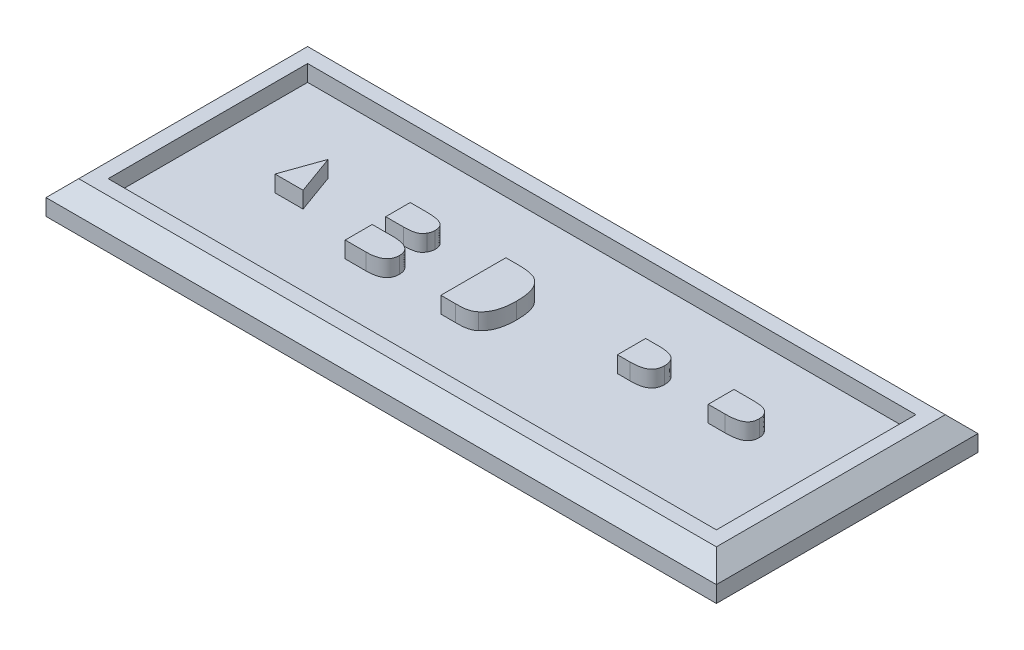
SolidWorks part; units mm, degrees
material "BUTYL"
ref_plane "Front Plane" through (0, 0, 0) normal (0, 0, 1) x (1, 0, 0)
ref_plane "Top Plane" through (0, 0, 0) normal (0, 1, 0) x (1, 0, 0)
ref_plane "Right Plane" through (0, 0, 0) normal (1, 0, 0) x (0, 0, -1)
sketch "Sketch1" plane through (0, 0, 0) normal (0, 1, 0) x (1, 0, 0)
  line L1 (20.5, -8) -> (-20.5, -8)
  line L2 (20.5, -8) -> (20.5, 8)
  line L3 (20.5, 8) -> (-20.5, 8)
  line L4 (-20.5, -8) -> (-20.5, 8)
  line L5 (20.5, -8) -> (-20.5, 8) construction
  line L6 (20.5, 8) -> (-20.5, -8) construction
  point P0 (0, 0)
  dimension "D1" = 41
  dimension "D2" = 16
extrude "Boss-Extrude1" add sketch "Sketch1" along normal blind 2
chamfer "Chamfer1" distance 1 angle 45 4 edges at (0, 2, -8) (20.5, 2, 0) (0, 2, 8) (-20.5, 2, 0)
sketch "Sketch2" plane through (0, 2, 0) normal (0, 1, 0) x (1, 0, 0)
  line L0 (-20.5, 8) -> (20.5, 8) construction
  line L1 (18.6, -6.1) -> (-18.6, -6.1)
  line L2 (18.6, -6.1) -> (18.6, 6.1)
  line L3 (18.6, 6.1) -> (-18.6, 6.1)
  line L4 (-18.6, -6.1) -> (-18.6, 6.1)
  line L5 (18.6, -6.1) -> (-18.6, 6.1) construction
  line L6 (18.6, 6.1) -> (-18.6, -6.1) construction
  line L7 (-20.5, -8) -> (-20.5, 8) construction
  point P0 (0, 0)
  dimension "D1" = 1.9
  dimension "D2" = 1.9
extrude "Cut-Extrude1" cut sketch "Sketch2" against normal blind 1
sketch "Sketch3" plane through (0, 1, 0) normal (0, 1, 0) x (1, 0, 0)
  line L0 (-17.5, -3) -> (17.5, -3) construction
  text T0 "ABDIPR" font "Arial Rounded MT Bold" height 6
  point P3 (0, -3)
  dimension "D1" = 35
  dimension "D2" = 3
extrude "Boss-Extrude2" add sketch "Sketch3" along normal blind 0.1
sketch "Sketch5" plane through (0, 1, 0) normal (0, 1, 0) x (1, 0, 0)
  line L0 (12.7688, 1.875) -> (11.7, 1.875) construction
  line L1 (11.7, 1.875) -> (11.7, 0.3) construction
  line L2 (11.7, 0.3) -> (12.7371, 0.3) construction
  line L3 (-12.8941, 1.65) -> (-13.7437, -0.75)
  line L4 (-13.7437, -0.75) -> (-12.0281, -0.75)
  line L5 (-12.0281, -0.75) -> (-12.8941, 1.65)
  line L6 (-12.8941, 1.65) -> (-13.7437, -0.75)
  line L7 (-13.7437, -0.75) -> (-12.0281, -0.75)
  line L8 (-12.0281, -0.75) -> (-12.8941, 1.65)
  line L9 (7.0793, 1.875) -> (6.3, 1.875) construction
  line L10 (6.3, 1.875) -> (6.3, 0.15) construction
  line L11 (6.3, 0.15) -> (7.0793, 0.15) construction
  line L12 (-1.4648, 1.875) -> (-2.25, 1.875) construction
  line L13 (-2.25, 1.875) -> (-2.25, -2.1) construction
  line L14 (-2.25, -2.1) -> (-1.3488, -2.1) construction
  line L15 (-6.866, -0.45) -> (-8.1, -0.45) construction
  line L16 (-8.1, -0.45) -> (-8.1, -2.1) construction
  line L17 (-8.1, -2.1) -> (-6.8262, -2.1) construction
  line L18 (-7.1367, 1.875) -> (-8.1, 1.875) construction
  line L19 (-8.1, 1.875) -> (-8.1, 0.375) construction
  line L20 (-8.1, 0.375) -> (-7.0137, 0.375) construction
  line L21 (12.7688, 1.875) -> (11.7, 1.875)
  line L22 (11.7, 1.875) -> (11.7, 0.3)
  line L23 (11.7, 0.3) -> (12.7371, 0.3)
  line L24 (7.0793, 1.875) -> (6.3, 1.875)
  line L25 (6.3, 1.875) -> (6.3, 0.15)
  line L26 (6.3, 0.15) -> (7.0793, 0.15)
  line L27 (-1.4648, 1.875) -> (-2.25, 1.875)
  line L28 (-2.25, 1.875) -> (-2.25, -2.1)
  line L29 (-2.25, -2.1) -> (-1.3488, -2.1)
  line L30 (-6.866, -0.45) -> (-8.1, -0.45)
  line L31 (-8.1, -0.45) -> (-8.1, -2.1)
  line L32 (-8.1, -2.1) -> (-6.8262, -2.1)
  line L33 (-7.1367, 1.875) -> (-8.1, 1.875)
  line L34 (-8.1, 1.875) -> (-8.1, 0.375)
  line L35 (-8.1, 0.375) -> (-7.0137, 0.375)
  spline S0 degree 3 poles (636.1641, 1902.3115) (13.4565, -15.0711) (15.9902, 1.1964) (13.4389, 1.8288) (13.3568, 1.8418) (13.2632, 1.8553) (13.1572, 1.8644) (13.0387, 1.8693) (6.9662, 2.1272) (0.5827, -14.141) (37.3484, 2001.6396) knots -9.463288 -9.463288 -9.463288 -9.463288 0.075159 0.163378 0.266297 0.383318 0.514253 0.660795 0.8232 23.058791 23.058791 23.058791 23.058791 only from (13.5691, 1.7895) to (12.7688, 1.875) construction
  spline S1 degree 3 poles (53.3008, -1999.2151) (-1.5912, 19.4596) (6.0427, -0.1571) (13.117, 0.3151) (13.285, 0.3372) (13.4361, 0.3681) (13.572, 0.4091) (13.6895, 0.4663) (13.793, 0.5325) (13.8776, 0.6151) (13.9457, 0.7122) (13.9917, 0.8268) (14.8069, 4.518) (-12.1459, 11.1207) (2003.8058, -199.5267) knots -11.98143 -11.98143 -11.98143 -11.98143 0.116004 0.22342 0.320583 0.409966 0.491045 0.566273 0.636247 0.703392 0.770177 0.84071 0.916405 7.297933 7.297933 7.297933 7.297933 only from (12.7371, 0.3) to (14.025, 1.0969) construction
  spline S2 degree 3 poles (2003.3668, 206.5207) (-10.522, -7.7795) (14.7098, -1.8463) (13.9972, 1.3213) (13.9595, 1.4242) (13.9065, 1.5187) (13.841, 1.6053) (13.7614, 1.6789) (11.1525, 3.5367) (-3.988, -17.2235) (977.1885, 1754.2872) knots -10.607515 -10.607515 -10.607515 -10.607515 0.13182 0.25825 0.380206 0.503359 0.625641 0.747872 0.871018 11.467851 11.467851 11.467851 11.467851 only from (14.025, 1.0969) to (13.5691, 1.7895) construction
  spline S3 degree 3 poles (1232.4253, 1582.9606) (-1.6719, -19.9023) (10.3794, 0.3213) (7.9441, 1.7387) (7.8387, 1.7791) (7.7189, 1.8166) (7.5819, 1.8419) (7.429, 1.862) (0.9477, 2.296) (-5.9865, -17.5415) (37.829, 2001.6036) knots -7.503764 -7.503764 -7.503764 -7.503764 0.084936 0.178562 0.282967 0.398901 0.527506 0.670084 0.828145 18.59632 18.59632 18.59632 18.59632 only from (8.1035, 1.6242) to (7.0793, 1.875) construction
  spline S4 degree 3 poles (51.2137, -1999.2957) (-6.4783, 19.9924) (0.7904, -0.3609) (7.4497, 0.168) (7.6125, 0.1953) (7.7595, 0.2304) (7.8902, 0.2792) (8.004, 0.3433) (8.1028, 0.4193) (8.1839, 0.5104) (8.2491, 0.6153) (8.2923, 0.7364) (9.0939, 4.6114) (-17.4307, 11.3013) (1998.5684, -195.6446) knots -11.235596 -11.235596 -11.235596 -11.235596 0.112942 0.216743 0.311985 0.398388 0.477984 0.552443 0.623708 0.692647 0.762442 0.836024 0.913978 7.58211 7.58211 7.58211 7.58211 only from (7.0793, 0.15) to (8.325, 1.016) construction
  spline S5 degree 3 poles (1992.4694, 252.0641) (-20.7902, -10.8673) (9.3304, -2.7158) (8.2752, 1.3544) (6.7551, 4.6626) (-21.8884, -10.2828) (1663.3677, 1123.9402) knots -18.152594 -18.152594 -18.152594 -18.152594 0.269525 0.519477 0.760623 16.57353 16.57353 16.57353 16.57353 only from (8.325, 1.016) to (8.1035, 1.6242) construction
  spline S6 degree 3 poles (-26.2033, -2001.8216) (-20.923, 7.3319) (-11.0131, -2.2517) (-1.089, -2.0971) (-0.9808, -2.0926) (-0.8559, -2.0838) (-0.7074, -2.0594) (-0.5621, -2.0173) (-0.4475, -1.9714) (-0.3661, -1.9297) (2.299, -0.2084) (-7.0697, 17.372) (1213.5859, -1591.3109) knots -24.772609 -24.772609 -24.772609 -24.772609 0.118496 0.223182 0.315098 0.392345 0.53942 0.694723 0.773569 0.851294 0.925516 8.774116 8.774116 8.774116 8.774116 only from (-1.3488, -2.1) to (-0.2227, -1.8246) construction
  spline S7 degree 3 poles (1458.0092, -1370.5595) (-28.495, 12.4431) (-2.688, -5.2763) (0.0437, -1.5264) (0.1476, -1.3426) (0.2322, -1.1356) (0.2953, -0.9055) (0.342, -0.6539) (1.1485, 7.1944) (-25.3575, 16.2492) (1998.9753, -71.7675) knots -6.991882 -6.991882 -6.991882 -6.991882 0.103775 0.209904 0.320807 0.437978 0.56343 0.698232 0.843267 13.052088 13.052088 13.052088 13.052088 only from (-0.2227, -1.8246) to (0.375, -0.0902) construction
  spline S8 degree 3 poles (1999.5964, 53.626) (-20.6716, -14.0404) (0.8434, -6.49) (0.3599, 0.312) (0.3415, 0.4954) (0.3113, 0.6645) (0.2764, 0.8209) (0.2301, 0.9628) (0.1781, 1.0922) (0.1152, 1.2071) (0.047, 1.3104) (-0.0248, 1.4036) (-0.1, 1.4871) (-0.1783, 1.5618) (-0.2621, 1.625) (-0.3492, 1.6792) (-0.4398, 1.7248) (-0.5695, 1.7694) (-0.7428, 1.8118) (-0.9656, 1.8495) (-8.4487, 2.5291) (-16.8553, -22.0263) (55.8382, 2000.9693) knots -6.307565 -6.307565 -6.307565 -6.307565 0.066635 0.129301 0.18771 0.24211 0.292941 0.340261 0.384153 0.425623 0.464852 0.502003 0.537582 0.571813 0.605015 0.637447 0.669407 0.70143 0.767873 0.839223 0.916594 7.918816 7.918816 7.918816 7.918816 only from (0.375, -0.0902) to (-1.4648, 1.875) construction
  spline S9 degree 3 poles (1988.1908, 155.6533) (-27.2091, -9.3668) (-5.1031, -4.2864) (-5.6432, -1.0658) (-5.6661, -0.9762) (-5.7, -0.8939) (-5.7449, -0.8194) (-5.8001, -0.7531) (-5.8631, -0.6927) (-5.9373, -0.6413) (-6.0198, -0.5948) (-6.1133, -0.5573) (-6.215, -0.5226) (-6.327, -0.4964) (-6.4479, -0.4754) (-6.5786, -0.46) (-13.2067, -0.11) (-20.1273, -15.6259) (16.0175, 1999.3482) knots -5.614546 -5.614546 -5.614546 -5.614546 0.061148 0.11878 0.17266 0.225256 0.276327 0.326632 0.378191 0.430965 0.486588 0.546018 0.609676 0.677526 0.750107 0.827684 0.911124 12.539007 12.539007 12.539007 12.539007 only from (-5.625, -1.2633) to (-6.866, -0.45) construction
  spline S10 degree 3 poles (42.2674, -2001.4539) (-18.545, 15.0307) (-12.2728, -2.4734) (-6.5477, -2.0887) (-6.4208, -2.0726) (-6.3031, -2.0489) (-6.1945, -2.0201) (-6.0946, -1.9855) (-6.0055, -1.9416) (-5.9253, -1.8924) (-5.8539, -1.8372) (-5.7929, -1.7746) (-5.7399, -1.7058) (-5.6986, -1.6295) (-5.6647, -1.5472) (-5.642, -1.458) (-5.1349, 1.8816) (-25.9508, 6.8281) (1989.1917, -144.6252) knots -10.094895 -10.094895 -10.094895 -10.094895 0.087365 0.169264 0.24597 0.3178 0.38563 0.448456 0.507993 0.564288 0.617972 0.67027 0.721547 0.773883 0.826332 0.881685 0.93936 6.90322 6.90322 6.90322 6.90322 only from (-6.8262, -2.1) to (-5.625, -1.2633) construction
  spline S11 degree 3 poles (54.5485, -1998.6106) (-19.9527, 23.2823) (-12.8388, -0.17) (-6.6289, 0.3933) (-6.4696, 0.4181) (-6.3324, 0.4531) (-6.2149, 0.506) (-6.1128, 0.5758) (-3.7431, 3.0992) (-23.5524, 21.3925) (1628.0032, -1152.489) knots -15.246108 -15.246108 -15.246108 -15.246108 0.175446 0.330768 0.465552 0.581967 0.686925 0.788884 0.892046 9.344296 9.344296 9.344296 9.344296 only from (-7.0137, 0.375) to (-5.9602, 0.7746) construction
  spline S12 degree 3 poles (1814.7329, -826.8127) (-29.9159, 5.5384) (-6.7734, -1.7747) (-5.8825, 0.9512) (-5.2338, 3.7986) (-29.5171, 9.5352) (1981.4611, -223.2727) knots -21.166705 -21.166705 -21.166705 -21.166705 0.246587 0.493901 0.741886 22.55561 22.55561 22.55561 22.55561 only from (-5.9602, 0.7746) to (-5.8582, 1.1473) construction
  spline S13 degree 3 poles (1988.8741, 145.9893) (-27.6799, -6.9201) (-5.3374, -1.9161) (-5.8761, 1.3461) (-5.9002, 1.4332) (-5.934, 1.5119) (-5.9796, 1.581) (-6.0346, 1.6413) (-6.1007, 1.6909) (-6.1758, 1.7324) (-6.2609, 1.7656) (-6.3558, 1.7948) (-6.4605, 1.8208) (-6.5762, 1.8397) (-6.7016, 1.8569) (-6.8374, 1.8662) (-13.0823, 2.1991) (-19.8338, -15.18) (36.8491, 2001.3395) knots -5.697941 -5.697941 -5.697941 -5.697941 0.062689 0.119775 0.173302 0.223466 0.271717 0.319978 0.368133 0.418283 0.472296 0.53062 0.595091 0.664304 0.739395 0.820357 0.906745 11.878665 11.878665 11.878665 11.878665 only from (-5.8582, 1.1473) to (-7.1367, 1.875) construction
  spline S14 degree 3 poles (13.5691, 1.7895) (13.5501, 1.7964) (13.5087, 1.8115) (13.4389, 1.8288) (13.3568, 1.8418) (13.2632, 1.8553) (13.1572, 1.8644) (13.0387, 1.8693) (12.9079, 1.8749) (12.8164, 1.875) (12.7688, 1.875) knots 0 0 0 0 0.075159 0.163378 0.266297 0.383318 0.514253 0.660795 0.8232 1 1 1 1
  spline S15 degree 3 poles (12.7371, 0.3) (12.8039, 0.301) (12.9326, 0.3028) (13.117, 0.3151) (13.285, 0.3372) (13.4361, 0.3681) (13.572, 0.4091) (13.6895, 0.4663) (13.793, 0.5325) (13.8776, 0.6151) (13.9457, 0.7122) (13.9917, 0.8268) (14.0204, 0.9568) (14.0234, 1.0487) (14.025, 1.0969) knots 0 0 0 0 0.116004 0.22342 0.320583 0.409966 0.491045 0.566273 0.636247 0.703392 0.770177 0.84071 0.916405 1 1 1 1
  spline S16 degree 3 poles (14.025, 1.0969) (14.0239, 1.1357) (14.0218, 1.2117) (13.9972, 1.3213) (13.9595, 1.4242) (13.9065, 1.5187) (13.841, 1.6053) (13.7614, 1.6789) (13.6713, 1.743) (13.6037, 1.7737) (13.5691, 1.7895) knots 0 0 0 0 0.13182 0.25825 0.380206 0.503359 0.625641 0.747872 0.871018 1 1 1 1
  spline S17 degree 3 poles (8.1035, 1.6242) (8.0807, 1.6445) (8.0326, 1.6872) (7.9441, 1.7387) (7.8387, 1.7791) (7.7189, 1.8166) (7.5819, 1.8419) (7.429, 1.862) (7.2595, 1.8734) (7.141, 1.8744) (7.0793, 1.875) knots 0 0 0 0 0.084936 0.178562 0.282967 0.398901 0.527506 0.670084 0.828145 1 1 1 1
  spline S18 degree 3 poles (7.0793, 0.15) (7.1446, 0.1513) (7.2698, 0.1537) (7.4497, 0.168) (7.6125, 0.1953) (7.7595, 0.2304) (7.8902, 0.2792) (8.004, 0.3433) (8.1028, 0.4193) (8.1839, 0.5104) (8.2491, 0.6153) (8.2923, 0.7364) (8.3202, 0.8714) (8.3234, 0.9663) (8.325, 1.016) knots 0 0 0 0 0.112942 0.216743 0.311985 0.398388 0.477984 0.552443 0.623708 0.692647 0.762442 0.836024 0.913978 1 1 1 1
  spline S19 degree 3 poles (8.325, 1.016) (8.3225, 1.0757) (8.3176, 1.1907) (8.2752, 1.3544) (8.2071, 1.5026) (8.1379, 1.5838) (8.1035, 1.6242) knots 0 0 0 0 0.269525 0.519477 0.760623 1 1 1 1
  spline S20 degree 3 poles (-1.3488, -2.1) (-1.302, -2.0997) (-1.2137, -2.0991) (-1.089, -2.0971) (-0.9808, -2.0926) (-0.8559, -2.0838) (-0.7074, -2.0594) (-0.5621, -2.0173) (-0.4475, -1.9714) (-0.3661, -1.9297) (-0.2907, -1.881) (-0.2453, -1.8434) (-0.2227, -1.8246) knots 0 0 0 0 0.118496 0.223182 0.315098 0.392345 0.53942 0.694723 0.773569 0.851294 0.925516 1 1 1 1
  spline S21 degree 3 poles (-0.2227, -1.8246) (-0.1742, -1.7804) (-0.0761, -1.6909) (0.0437, -1.5264) (0.1476, -1.3426) (0.2322, -1.1356) (0.2953, -0.9055) (0.342, -0.6539) (0.3701, -0.3795) (0.3733, -0.1891) (0.375, -0.0902) knots 0 0 0 0 0.103775 0.209904 0.320807 0.437978 0.56343 0.698232 0.843267 1 1 1 1
  spline S22 degree 3 poles (0.375, -0.0902) (0.3746, -0.0203) (0.3739, 0.1155) (0.3599, 0.312) (0.3415, 0.4954) (0.3113, 0.6645) (0.2764, 0.8209) (0.2301, 0.9628) (0.1781, 1.0922) (0.1152, 1.2071) (0.047, 1.3104) (-0.0248, 1.4036) (-0.1, 1.4871) (-0.1783, 1.5618) (-0.2621, 1.625) (-0.3492, 1.6792) (-0.4398, 1.7248) (-0.5695, 1.7694) (-0.7428, 1.8118) (-0.9656, 1.8495) (-1.2085, 1.8716) (-1.3773, 1.8738) (-1.4648, 1.875) knots 0 0 0 0 0.066635 0.129301 0.18771 0.24211 0.292941 0.340261 0.384153 0.425623 0.464852 0.502003 0.537582 0.571813 0.605015 0.637447 0.669407 0.70143 0.767873 0.839223 0.916594 1 1 1 1
  spline S23 degree 3 poles (-5.625, -1.2633) (-5.6257, -1.2288) (-5.6271, -1.1619) (-5.6432, -1.0658) (-5.6661, -0.9762) (-5.7, -0.8939) (-5.7449, -0.8194) (-5.8001, -0.7531) (-5.8631, -0.6927) (-5.9373, -0.6413) (-6.0198, -0.5948) (-6.1133, -0.5573) (-6.215, -0.5226) (-6.327, -0.4964) (-6.4479, -0.4754) (-6.5786, -0.46) (-6.7191, -0.4525) (-6.816, -0.4509) (-6.866, -0.45) knots 0 0 0 0 0.061148 0.11878 0.17266 0.225256 0.276327 0.326632 0.378191 0.430965 0.486588 0.546018 0.609676 0.677526 0.750107 0.827684 0.911124 1 1 1 1
  spline S24 degree 3 poles (-6.8262, -2.1) (-6.7777, -2.0993) (-6.6838, -2.0978) (-6.5477, -2.0887) (-6.4208, -2.0726) (-6.3031, -2.0489) (-6.1945, -2.0201) (-6.0946, -1.9855) (-6.0055, -1.9416) (-5.9253, -1.8924) (-5.8539, -1.8372) (-5.7929, -1.7746) (-5.7399, -1.7058) (-5.6986, -1.6295) (-5.6647, -1.5472) (-5.642, -1.458) (-5.6275, -1.3626) (-5.6258, -1.2969) (-5.625, -1.2633) knots 0 0 0 0 0.087365 0.169264 0.24597 0.3178 0.38563 0.448456 0.507993 0.564288 0.617972 0.67027 0.721547 0.773883 0.826332 0.881685 0.93936 1 1 1 1
  spline S25 degree 3 poles (-7.0137, 0.375) (-6.9441, 0.3755) (-6.8129, 0.3766) (-6.6289, 0.3933) (-6.4696, 0.4181) (-6.3324, 0.4531) (-6.2149, 0.506) (-6.1128, 0.5758) (-6.0271, 0.6671) (-5.9828, 0.7382) (-5.9602, 0.7746) knots 0 0 0 0 0.175446 0.330768 0.465552 0.581967 0.686925 0.788884 0.892046 1 1 1 1
  spline S26 degree 3 poles (-5.9602, 0.7746) (-5.9444, 0.8027) (-5.9127, 0.8589) (-5.8825, 0.9512) (-5.8606, 1.0474) (-5.859, 1.1135) (-5.8582, 1.1473) knots 0 0 0 0 0.246587 0.493901 0.741886 1 1 1 1
  spline S27 degree 3 poles (-5.8582, 1.1473) (-5.8589, 1.1825) (-5.8602, 1.2498) (-5.8761, 1.3461) (-5.9002, 1.4332) (-5.934, 1.5119) (-5.9796, 1.581) (-6.0346, 1.6413) (-6.1007, 1.6909) (-6.1758, 1.7324) (-6.2609, 1.7656) (-6.3558, 1.7948) (-6.4605, 1.8208) (-6.5762, 1.8397) (-6.7016, 1.8569) (-6.8374, 1.8662) (-6.9835, 1.8739) (-7.0844, 1.8746) (-7.1367, 1.875) knots 0 0 0 0 0.062689 0.119775 0.173302 0.223466 0.271717 0.319978 0.368133 0.418283 0.472296 0.53062 0.595091 0.664304 0.739395 0.820357 0.906745 1 1 1 1
  dimension "D1" = 0
extrude "Boss-Extrude3" add sketch "Sketch5" along normal up to surface (1 mm away) up to face at (0, 2, 0)
sketch "Sketch6" plane through (0, 2, 0) normal (0, 1, 0) x (1, 0, 0)
  line L0 (12.7688, 1.875) -> (11.7, 1.875) construction
  line L1 (11.7, 1.875) -> (11.7, 0.3) construction
  line L2 (11.7, 0.3) -> (12.7371, 0.3) construction
  line L3 (7.0793, 1.875) -> (6.3, 1.875) construction
  line L4 (6.3, 1.875) -> (6.3, 0.15) construction
  line L5 (6.3, 0.15) -> (7.0793, 0.15) construction
  line L6 (-1.4648, 1.875) -> (-2.25, 1.875) construction
  line L7 (-2.25, 1.875) -> (-2.25, -2.1) construction
  line L8 (-2.25, -2.1) -> (-1.3488, -2.1) construction
  line L9 (-8.1, -2.1) -> (-6.8262, -2.1) construction
  line L10 (-6.866, -0.45) -> (-8.1, -0.45) construction
  line L11 (-8.1, -0.45) -> (-8.1, -2.1) construction
  line L12 (-7.1367, 1.875) -> (-8.1, 1.875) construction
  line L13 (-8.1, 1.875) -> (-8.1, 0.375) construction
  line L14 (-8.1, 0.375) -> (-7.0137, 0.375) construction
  line L15 (-13.7437, -0.75) -> (-12.0281, -0.75) construction
  line L16 (-12.0281, -0.75) -> (-12.8941, 1.65) construction
  line L17 (-12.8941, 1.65) -> (-13.7437, -0.75) construction
  line L18 (12.7688, 1.875) -> (11.7, 1.875)
  line L19 (11.7, 1.875) -> (11.7, 0.3)
  line L20 (11.7, 0.3) -> (12.7371, 0.3)
  line L21 (7.0793, 1.875) -> (6.3, 1.875)
  line L22 (6.3, 1.875) -> (6.3, 0.15)
  line L23 (6.3, 0.15) -> (7.0793, 0.15)
  line L24 (-1.4648, 1.875) -> (-2.25, 1.875)
  line L25 (-2.25, 1.875) -> (-2.25, -2.1)
  line L26 (-2.25, -2.1) -> (-1.3488, -2.1)
  line L27 (-8.1, -2.1) -> (-6.8262, -2.1)
  line L28 (-6.866, -0.45) -> (-8.1, -0.45)
  line L29 (-8.1, -0.45) -> (-8.1, -2.1)
  line L30 (-7.1367, 1.875) -> (-8.1, 1.875)
  line L31 (-8.1, 1.875) -> (-8.1, 0.375)
  line L32 (-8.1, 0.375) -> (-7.0137, 0.375)
  line L33 (-13.7437, -0.75) -> (-12.0281, -0.75)
  line L34 (-12.0281, -0.75) -> (-12.8941, 1.65)
  line L35 (-12.8941, 1.65) -> (-13.7437, -0.75)
  line L36 (18.6, -6.1) -> (18.6, 6.1) construction
  line L37 (-18.6, -6.1) -> (18.6, -6.1) construction
  line L38 (-18.6, 6.1) -> (-18.6, -6.1) construction
  line L39 (18.6, 6.1) -> (-18.6, 6.1) construction
  line L40 (18.6, -6.1) -> (18.6, 6.1)
  line L41 (-18.6, -6.1) -> (18.6, -6.1)
  line L42 (-18.6, 6.1) -> (-18.6, -6.1)
  line L43 (18.6, 6.1) -> (-18.6, 6.1)
  spline S0 degree 3 poles (26.9398, -999.5974) (1.4754, 12.3382) (7.464, -0.0622) (13.117, 0.3151) (13.285, 0.3372) (13.4361, 0.3681) (13.572, 0.4091) (13.6895, 0.4663) (13.793, 0.5325) (13.8776, 0.6151) (13.9457, 0.7122) (13.9917, 0.8268) (14.6447, 3.7836) (-2.4262, 8.5839) (1009.2792, -96.0414) knots -9.509835 -9.509835 -9.509835 -9.509835 0.116004 0.22342 0.320583 0.409966 0.491045 0.566273 0.636247 0.703392 0.770177 0.84071 0.916405 5.999107 5.999107 5.999107 5.999107 only from (12.7371, 0.3) to (14.025, 1.0969) construction
  spline S1 degree 3 poles (1009.0137, 101.0826) (-1.4133, -5.5039) (14.5679, -1.2156) (13.9972, 1.3213) (13.9595, 1.4242) (13.9065, 1.5187) (13.841, 1.6053) (13.7614, 1.6789) (11.672, 3.1668) (1.6009, -9.7782) (493.0101, 879.351) knots -8.419873 -8.419873 -8.419873 -8.419873 0.13182 0.25825 0.380206 0.503359 0.625641 0.747872 0.871018 9.308938 9.308938 9.308938 9.308938 only from (14.025, 1.0969) to (13.5691, 1.7895) construction
  spline S2 degree 3 poles (327.016, 951.3933) (14.2761, -9.1172) (15.4783, 1.3232) (13.4389, 1.8288) (13.3568, 1.8418) (13.2632, 1.8553) (13.1572, 1.8644) (13.0387, 1.8693) (8.1919, 2.0752) (3.1619, -8.2131) (19.8202, 1001.8495) knots -7.511319 -7.511319 -7.511319 -7.511319 0.075159 0.163378 0.266297 0.383318 0.514253 0.660795 0.8232 18.508582 18.508582 18.508582 18.508582 only from (13.5691, 1.7895) to (12.7688, 1.875) construction
  spline S3 degree 3 poles (23.4275, -999.7155) (-3.5633, 12.6091) (2.1271, -0.2547) (7.4497, 0.168) (7.6125, 0.1953) (7.7595, 0.2304) (7.8902, 0.2792) (8.004, 0.3433) (8.1028, 0.4193) (8.1839, 0.5104) (8.2491, 0.6153) (8.2923, 0.7364) (8.9343, 3.8401) (-7.8621, 8.7246) (1003.7932, -93.9832) knots -8.91779 -8.91779 -8.91779 -8.91779 0.112942 0.216743 0.311985 0.398388 0.477984 0.552443 0.623708 0.692647 0.762442 0.836024 0.913978 6.224636 6.224636 6.224636 6.224636 only from (7.0793, 0.15) to (8.325, 1.016) construction
  spline S4 degree 3 poles (1000.8515, 123.039) (-9.9655, -7.765) (9.1215, -1.9102) (8.2752, 1.3544) (7.0545, 4.011) (-11.5155, -5.0321) (834.0653, 565.3055) knots -14.409197 -14.409197 -14.409197 -14.409197 0.269525 0.519477 0.760623 13.362227 13.362227 13.362227 13.362227 only from (8.325, 1.016) to (8.1035, 1.6242) construction
  spline S5 degree 3 poles (622.1702, 790.8773) (2.597, -12.5181) (9.8954, 0.603) (7.9441, 1.7387) (7.8387, 1.7791) (7.7189, 1.8166) (7.5819, 1.8419) (7.429, 1.862) (2.2497, 2.2088) (-3.1989, -10.3387) (16.8855, 1001.8268) knots -5.956155 -5.956155 -5.956155 -5.956155 0.084936 0.178562 0.282967 0.398901 0.527506 0.670084 0.828145 14.966385 14.966385 14.966385 14.966385 only from (8.1035, 1.6242) to (7.0793, 1.875) construction
  spline S6 degree 3 poles (726.2419, -689.0284) (-19.0881, 6.2063) (-2.1494, -4.5369) (0.0437, -1.5264) (0.1476, -1.3426) (0.2322, -1.1356) (0.2953, -0.9055) (0.342, -0.6539) (0.9879, 5.6323) (-15.796, 12.6575) (999.9469, -29.2349) knots -5.550033 -5.550033 -5.550033 -5.550033 0.103775 0.209904 0.320807 0.437978 0.56343 0.698232 0.843267 10.566257 10.566257 10.566257 10.566257 only from (-0.2227, -1.8246) to (0.375, -0.0902) construction
  spline S7 degree 3 poles (1000.152, 20.938) (-12.8729, -11.0213) (0.7465, -5.1275) (0.3599, 0.312) (0.3415, 0.4954) (0.3113, 0.6645) (0.2764, 0.8209) (0.2301, 0.9628) (0.1781, 1.0922) (0.1152, 1.2071) (0.047, 1.3104) (-0.0248, 1.4036) (-0.1, 1.4871) (-0.1783, 1.5618) (-0.2621, 1.625) (-0.3492, 1.6792) (-0.4398, 1.7248) (-0.5695, 1.7694) (-0.7428, 1.8118) (-0.9656, 1.8495) (-6.9553, 2.3934) (-13.5066, -13.1515) (20.7917, 1001.6208) knots -5.006542 -5.006542 -5.006542 -5.006542 0.066635 0.129301 0.18771 0.24211 0.292941 0.340261 0.384153 0.425623 0.464852 0.502003 0.537582 0.571813 0.605015 0.637447 0.669407 0.70143 0.767873 0.839223 0.916594 6.491674 6.491674 6.491674 6.491674 only from (0.375, -0.0902) to (-1.4648, 1.875) construction
  spline S8 degree 3 poles (-22.4098, -1001.8777) (-16.8709, 3.8195) (-8.9911, -2.2202) (-1.089, -2.0971) (-0.9808, -2.0926) (-0.8559, -2.0838) (-0.7074, -2.0594) (-0.5621, -2.0173) (-0.4475, -1.9714) (-0.3661, -1.9297) (1.7649, -0.5534) (-3.7691, 10.9058) (608.829, -794.9159) knots -19.661105 -19.661105 -19.661105 -19.661105 0.118496 0.223182 0.315098 0.392345 0.53942 0.694723 0.773569 0.851294 0.925516 7.170525 7.170525 7.170525 7.170525 only from (-1.3488, -2.1) to (-0.2227, -1.8246) construction
  spline S9 degree 3 poles (12.7893, -1001.9074) (-16.0242, 8.6643) (-11.1199, -2.3959) (-6.5477, -2.0887) (-6.4208, -2.0726) (-6.3031, -2.0489) (-6.1945, -2.0201) (-6.0946, -1.9855) (-6.0055, -1.9416) (-5.9253, -1.8924) (-5.8539, -1.8372) (-5.7929, -1.7746) (-5.7399, -1.7058) (-5.6986, -1.6295) (-5.6647, -1.5472) (-5.642, -1.458) (-5.2365, 1.2124) (-18.404, 4.8946) (991.9827, -70.0674) knots -8.012471 -8.012471 -8.012471 -8.012471 0.087365 0.169264 0.24597 0.3178 0.38563 0.448456 0.507993 0.564288 0.617972 0.67027 0.721547 0.773883 0.826332 0.881685 0.93936 5.685588 5.685588 5.685588 5.685588 only from (-6.8262, -2.1) to (-5.625, -1.2633) construction
  spline S10 degree 3 poles (991.5058, 74.4216) (-19.2027, -7.3916) (-5.2112, -3.642) (-5.6432, -1.0658) (-5.6661, -0.9762) (-5.7, -0.8939) (-5.7449, -0.8194) (-5.8001, -0.7531) (-5.8631, -0.6927) (-5.9373, -0.6413) (-6.0198, -0.5948) (-6.1133, -0.5573) (-6.215, -0.5226) (-6.327, -0.4964) (-6.4479, -0.4754) (-6.5786, -0.46) (-11.8683, -0.1806) (-17.3277, -9.9736) (-1.145, 999.5332) knots -4.456516 -4.456516 -4.456516 -4.456516 0.061148 0.11878 0.17266 0.225256 0.276327 0.326632 0.378191 0.430965 0.486588 0.546018 0.609676 0.677526 0.750107 0.827684 0.911124 10.15847 10.15847 10.15847 10.15847 only from (-5.625, -1.2633) to (-6.866, -0.45) construction
  spline S11 degree 3 poles (903.3984, -415.2369) (-21.4919, 2.9972) (-6.5959, -1.2315) (-5.8825, 0.9512) (-5.3631, 3.2312) (-20.7426, 7.3419) (988.09, -108.6073) knots -16.801299 -16.801299 -16.801299 -16.801299 0.246587 0.493901 0.741886 18.11001 18.11001 18.11001 18.11001 only from (-5.9602, 0.7746) to (-5.8582, 1.1473) construction
  spline S12 degree 3 poles (991.7122, 70.7585) (-19.5865, -4.9706) (-5.4452, -1.2631) (-5.8761, 1.3461) (-5.9002, 1.4332) (-5.934, 1.5119) (-5.9796, 1.581) (-6.0346, 1.6413) (-6.1007, 1.6909) (-6.1758, 1.7324) (-6.2609, 1.7656) (-6.3558, 1.7948) (-6.4605, 1.8208) (-6.5762, 1.8397) (-6.7016, 1.8569) (-6.8374, 1.8662) (-11.8243, 2.132) (-17.1164, -8.8559) (9.477, 1001.729) knots -4.522686 -4.522686 -4.522686 -4.522686 0.062689 0.119775 0.173302 0.223466 0.271717 0.319978 0.368133 0.418283 0.472296 0.53062 0.595091 0.664304 0.739395 0.820357 0.906745 9.634646 9.634646 9.634646 9.634646 only from (-5.8582, 1.1473) to (-7.1367, 1.875) construction
  spline S13 degree 3 poles (18.4454, -999.2998) (-17.1194, 14.7917) (-11.5959, -0.0573) (-6.6289, 0.3933) (-6.4696, 0.4181) (-6.3324, 0.4531) (-6.2149, 0.506) (-6.1128, 0.5758) (-4.2142, 2.5976) (-16.4789, 14.6719) (812.6976, -573.4737) knots -12.101409 -12.101409 -12.101409 -12.101409 0.175446 0.330768 0.465552 0.581967 0.686925 0.788884 0.892046 7.623233 7.623233 7.623233 7.623233 only from (-7.0137, 0.375) to (-5.9602, 0.7746) construction
  spline S14 degree 3 poles (12.7371, 0.3) (12.8039, 0.301) (12.9326, 0.3028) (13.117, 0.3151) (13.285, 0.3372) (13.4361, 0.3681) (13.572, 0.4091) (13.6895, 0.4663) (13.793, 0.5325) (13.8776, 0.6151) (13.9457, 0.7122) (13.9917, 0.8268) (14.0204, 0.9568) (14.0234, 1.0487) (14.025, 1.0969) knots 0 0 0 0 0.116004 0.22342 0.320583 0.409966 0.491045 0.566273 0.636247 0.703392 0.770177 0.84071 0.916405 1 1 1 1
  spline S15 degree 3 poles (14.025, 1.0969) (14.0239, 1.1357) (14.0218, 1.2117) (13.9972, 1.3213) (13.9595, 1.4242) (13.9065, 1.5187) (13.841, 1.6053) (13.7614, 1.6789) (13.6713, 1.743) (13.6037, 1.7737) (13.5691, 1.7895) knots 0 0 0 0 0.13182 0.25825 0.380206 0.503359 0.625641 0.747872 0.871018 1 1 1 1
  spline S16 degree 3 poles (13.5691, 1.7895) (13.5501, 1.7964) (13.5087, 1.8115) (13.4389, 1.8288) (13.3568, 1.8418) (13.2632, 1.8553) (13.1572, 1.8644) (13.0387, 1.8693) (12.9079, 1.8749) (12.8164, 1.875) (12.7688, 1.875) knots 0 0 0 0 0.075159 0.163378 0.266297 0.383318 0.514253 0.660795 0.8232 1 1 1 1
  spline S17 degree 3 poles (7.0793, 0.15) (7.1446, 0.1513) (7.2698, 0.1537) (7.4497, 0.168) (7.6125, 0.1953) (7.7595, 0.2304) (7.8902, 0.2792) (8.004, 0.3433) (8.1028, 0.4193) (8.1839, 0.5104) (8.2491, 0.6153) (8.2923, 0.7364) (8.3202, 0.8714) (8.3234, 0.9663) (8.325, 1.016) knots 0 0 0 0 0.112942 0.216743 0.311985 0.398388 0.477984 0.552443 0.623708 0.692647 0.762442 0.836024 0.913978 1 1 1 1
  spline S18 degree 3 poles (8.325, 1.016) (8.3225, 1.0757) (8.3176, 1.1907) (8.2752, 1.3544) (8.2071, 1.5026) (8.1379, 1.5838) (8.1035, 1.6242) knots 0 0 0 0 0.269525 0.519477 0.760623 1 1 1 1
  spline S19 degree 3 poles (8.1035, 1.6242) (8.0807, 1.6445) (8.0326, 1.6872) (7.9441, 1.7387) (7.8387, 1.7791) (7.7189, 1.8166) (7.5819, 1.8419) (7.429, 1.862) (7.2595, 1.8734) (7.141, 1.8744) (7.0793, 1.875) knots 0 0 0 0 0.084936 0.178562 0.282967 0.398901 0.527506 0.670084 0.828145 1 1 1 1
  spline S20 degree 3 poles (-0.2227, -1.8246) (-0.1742, -1.7804) (-0.0761, -1.6909) (0.0437, -1.5264) (0.1476, -1.3426) (0.2322, -1.1356) (0.2953, -0.9055) (0.342, -0.6539) (0.3701, -0.3795) (0.3733, -0.1891) (0.375, -0.0902) knots 0 0 0 0 0.103775 0.209904 0.320807 0.437978 0.56343 0.698232 0.843267 1 1 1 1
  spline S21 degree 3 poles (0.375, -0.0902) (0.3746, -0.0203) (0.3739, 0.1155) (0.3599, 0.312) (0.3415, 0.4954) (0.3113, 0.6645) (0.2764, 0.8209) (0.2301, 0.9628) (0.1781, 1.0922) (0.1152, 1.2071) (0.047, 1.3104) (-0.0248, 1.4036) (-0.1, 1.4871) (-0.1783, 1.5618) (-0.2621, 1.625) (-0.3492, 1.6792) (-0.4398, 1.7248) (-0.5695, 1.7694) (-0.7428, 1.8118) (-0.9656, 1.8495) (-1.2085, 1.8716) (-1.3773, 1.8738) (-1.4648, 1.875) knots 0 0 0 0 0.066635 0.129301 0.18771 0.24211 0.292941 0.340261 0.384153 0.425623 0.464852 0.502003 0.537582 0.571813 0.605015 0.637447 0.669407 0.70143 0.767873 0.839223 0.916594 1 1 1 1
  spline S22 degree 3 poles (-1.3488, -2.1) (-1.302, -2.0997) (-1.2137, -2.0991) (-1.089, -2.0971) (-0.9808, -2.0926) (-0.8559, -2.0838) (-0.7074, -2.0594) (-0.5621, -2.0173) (-0.4475, -1.9714) (-0.3661, -1.9297) (-0.2907, -1.881) (-0.2453, -1.8434) (-0.2227, -1.8246) knots 0 0 0 0 0.118496 0.223182 0.315098 0.392345 0.53942 0.694723 0.773569 0.851294 0.925516 1 1 1 1
  spline S23 degree 3 poles (-6.8262, -2.1) (-6.7777, -2.0993) (-6.6838, -2.0978) (-6.5477, -2.0887) (-6.4208, -2.0726) (-6.3031, -2.0489) (-6.1945, -2.0201) (-6.0946, -1.9855) (-6.0055, -1.9416) (-5.9253, -1.8924) (-5.8539, -1.8372) (-5.7929, -1.7746) (-5.7399, -1.7058) (-5.6986, -1.6295) (-5.6647, -1.5472) (-5.642, -1.458) (-5.6275, -1.3626) (-5.6258, -1.2969) (-5.625, -1.2633) knots 0 0 0 0 0.087365 0.169264 0.24597 0.3178 0.38563 0.448456 0.507993 0.564288 0.617972 0.67027 0.721547 0.773883 0.826332 0.881685 0.93936 1 1 1 1
  spline S24 degree 3 poles (-5.625, -1.2633) (-5.6257, -1.2288) (-5.6271, -1.1619) (-5.6432, -1.0658) (-5.6661, -0.9762) (-5.7, -0.8939) (-5.7449, -0.8194) (-5.8001, -0.7531) (-5.8631, -0.6927) (-5.9373, -0.6413) (-6.0198, -0.5948) (-6.1133, -0.5573) (-6.215, -0.5226) (-6.327, -0.4964) (-6.4479, -0.4754) (-6.5786, -0.46) (-6.7191, -0.4525) (-6.816, -0.4509) (-6.866, -0.45) knots 0 0 0 0 0.061148 0.11878 0.17266 0.225256 0.276327 0.326632 0.378191 0.430965 0.486588 0.546018 0.609676 0.677526 0.750107 0.827684 0.911124 1 1 1 1
  spline S25 degree 3 poles (-5.9602, 0.7746) (-5.9444, 0.8027) (-5.9127, 0.8589) (-5.8825, 0.9512) (-5.8606, 1.0474) (-5.859, 1.1135) (-5.8582, 1.1473) knots 0 0 0 0 0.246587 0.493901 0.741886 1 1 1 1
  spline S26 degree 3 poles (-5.8582, 1.1473) (-5.8589, 1.1825) (-5.8602, 1.2498) (-5.8761, 1.3461) (-5.9002, 1.4332) (-5.934, 1.5119) (-5.9796, 1.581) (-6.0346, 1.6413) (-6.1007, 1.6909) (-6.1758, 1.7324) (-6.2609, 1.7656) (-6.3558, 1.7948) (-6.4605, 1.8208) (-6.5762, 1.8397) (-6.7016, 1.8569) (-6.8374, 1.8662) (-6.9835, 1.8739) (-7.0844, 1.8746) (-7.1367, 1.875) knots 0 0 0 0 0.062689 0.119775 0.173302 0.223466 0.271717 0.319978 0.368133 0.418283 0.472296 0.53062 0.595091 0.664304 0.739395 0.820357 0.906745 1 1 1 1
  spline S27 degree 3 poles (-7.0137, 0.375) (-6.9441, 0.3755) (-6.8129, 0.3766) (-6.6289, 0.3933) (-6.4696, 0.4181) (-6.3324, 0.4531) (-6.2149, 0.506) (-6.1128, 0.5758) (-6.0271, 0.6671) (-5.9828, 0.7382) (-5.9602, 0.7746) knots 0 0 0 0 0.175446 0.330768 0.465552 0.581967 0.686925 0.788884 0.892046 1 1 1 1
extrude "Cut-Extrude2" cut sketch "Sketch6" against normal up to surface (1 mm away) up to face at (12.8991, 1, 0.3832)
